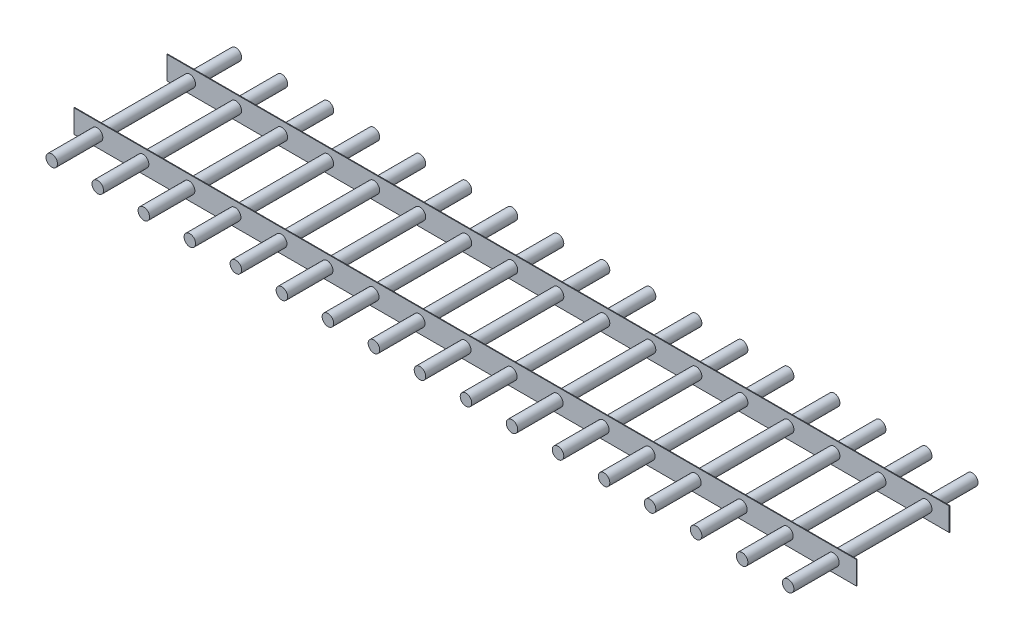
SolidWorks part; units mm, degrees
ref_plane "Front Plane" through (0, 0, 0) normal (0, 0, 1) x (1, 0, 0)
ref_plane "Top Plane" through (0, 0, 0) normal (0, 1, 0) x (1, 0, 0)
ref_plane "Right Plane" through (0, 0, 0) normal (1, 0, 0) x (0, 0, -1)
sketch "Sketch1" plane through (0, 0, 0) normal (0, 0, 1) x (1, 0, 0)
  line L0 (0, 0) -> (25.4, 0) construction
  circle A0 centre (0, 0) radius 3.175
  circle A1 centre (25.4, 0) radius 3.175
  circle A2 centre (50.8, 0) radius 3.175
  circle A3 centre (76.2, 0) radius 3.175
  circle A4 centre (101.6, 0) radius 3.175
  circle A5 centre (127, 0) radius 3.175
  circle A6 centre (152.4, 0) radius 3.175
  circle A7 centre (177.8, 0) radius 3.175
  circle A8 centre (203.2, 0) radius 3.175
  circle A9 centre (228.6, 0) radius 3.175
  circle A10 centre (254, 0) radius 3.175
  circle A11 centre (279.4, 0) radius 3.175
  circle A12 centre (304.8, 0) radius 3.175
  circle A13 centre (330.2, 0) radius 3.175
  circle A14 centre (355.6, 0) radius 3.175
  circle A15 centre (381, 0) radius 3.175
  circle A16 centre (406.4, 0) radius 3.175
  dimension "D1" = 6.35
  dimension "D2" = 25.4
extrude "Boss-Extrude1" add sketch "Sketch1" along normal mid plane 101.6
ref_plane "Plane1" through (0, 0, 25.4) normal (0, 0, 1) x (1, 0, 0)
sketch "Sketch2" plane through (0, 0, 25.4) normal (0, 0, 1) x (1, 0, 0)
  line L0 (0, 0) -> (-12.7, 0) construction
  line L1 (-12.7, 6.35) -> (419.1, 6.35)
  line L2 (-12.7, 6.35) -> (-12.7, -6.35)
  line L3 (-12.7, -6.35) -> (419.1, -6.35)
  line L4 (419.1, 6.35) -> (419.1, -6.35)
  line L5 (406.4, 0) -> (419.1, 0) construction
  dimension "D1" = 12.7
  dimension "D2" = 12.7
  dimension "D3" = 12.7
extrude "Boss-Extrude2" add sketch "Sketch2" along normal blind 0.381
mirror "Mirror1" about plane through (0, 0, 0) normal (0, 0, 1) of "Boss-Extrude2"
